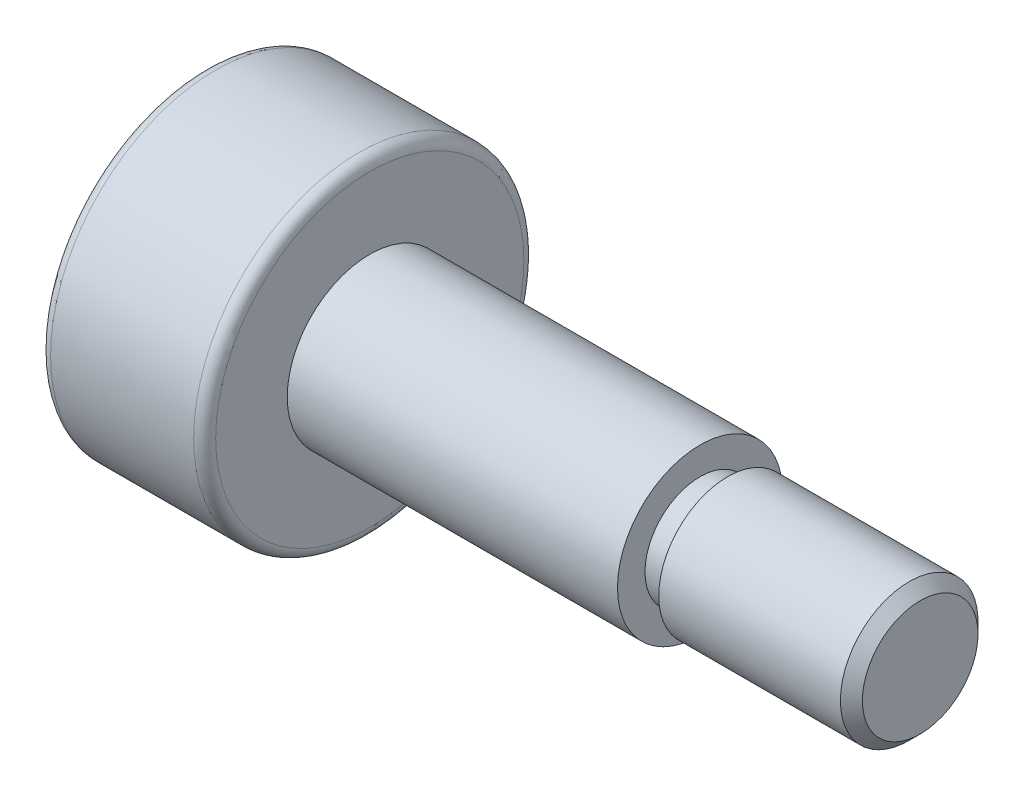
SolidWorks part; units mm, degrees
ref_plane "前视基准面" through (0, 0, 0) normal (0, 0, 1) x (1, 0, 0)
ref_plane "上视基准面" through (0, 0, 0) normal (0, 1, 0) x (1, 0, 0)
ref_plane "右视基准面" through (0, 0, 0) normal (1, 0, 0) x (0, 0, -1)
sketch "草图1" plane through (0, 0, 0) normal (0, 0, 1) x (1, 0, 0)
  line L0 (-6.5, 0) -> (6.5, 0) construction
  line L1 (-6.5, 0) -> (-6.5, 3)
  line L2 (-6.5, 3) -> (-3.5, 3)
  line L3 (-3.5, 3) -> (-3.5, 1.5)
  line L4 (-3.5, 1.5) -> (2.5, 1.5)
  line L5 (2.5, 1.5) -> (2.5, 1.25)
  line L6 (2.5, 1.25) -> (6.5, 1.25)
  line L7 (6.5, 1.25) -> (6.5, 0)
  line L8 (-6.5, 0) -> (6.5, 0)
  dimension "D1" = 3
  dimension "D2" = 6
  dimension "D3" = 2.5
  dimension "D4" = 4
  dimension "D5" = 6
  dimension "D6" = 3
revolve "旋转1" add sketch "草图1" angle 360 about L0
fillet "圆角1" radius 0.2 2 edges at (-3.5, 0, 3) (-6.5, 0, 3)
chamfer "倒角1" distance 0.2 angle 45 1 edges at (6.5, 0, 1.25)
sketch "草图3" plane through (0, 0, 0) normal (0, 0, 1) x (1, 0, 0)
  line L0 (2.5, 0) -> (6.3, 0) construction
  line L1 (2.5, -1.25) -> (2.5, 1.25) construction
  line L2 (6.3, 1.25) -> (6.3, -1.25) construction
  line L3 (2.5, -1.5) -> (2.5, 1.5) construction
  line L4 (2.5, 1.25) -> (3, 1.25)
  line L5 (2.5, 1.25) -> (2.5, 1)
  line L6 (2.5, 1) -> (3, 1)
  line L7 (3, 1.25) -> (3, 1)
  line L8 (6.3, 1.25) -> (2.5, 1.25) construction
  dimension "D1" = 2
  dimension "D2" = 0.5
revolve "切除-旋转1" cut sketch "草图3" angle 360 about L0
sketch "草图4" plane through (-6.5, 0, 0) normal (-1, 0, 0) x (0, 0, 1)
  line L1 (1.7321, 0) -> (0.866, 1.5)
  line L2 (0.866, 1.5) -> (-0.866, 1.5)
  line L3 (-0.866, 1.5) -> (-1.7321, 0)
  line L4 (-1.7321, 0) -> (-0.866, -1.5)
  line L5 (-0.866, -1.5) -> (0.866, -1.5)
  line L6 (0.866, -1.5) -> (1.7321, 0)
  circle A0 centre (0, 0) radius 1.5 construction
  dimension "D1" = 3
extrude "切除-拉伸1" cut sketch "草图4" against normal blind 2
